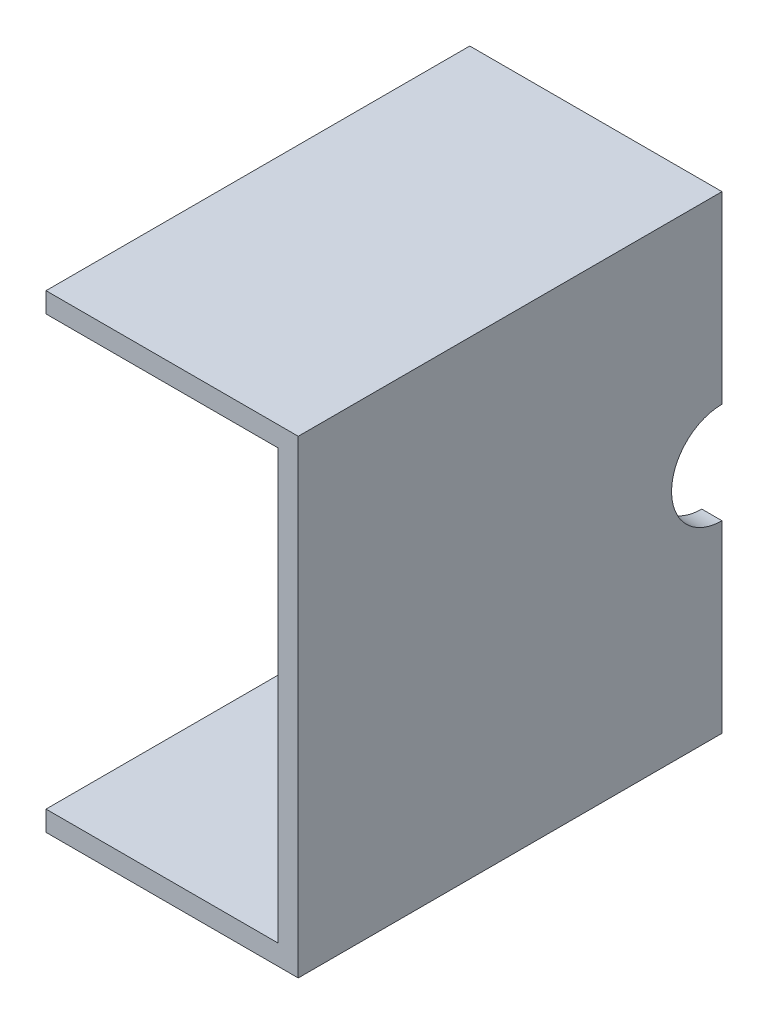
SolidWorks part; units mm, degrees
ref_plane "Front Plane" through (0, 0, 0) normal (0, 0, 1) x (1, 0, 0)
ref_plane "Top Plane" through (0, 0, 0) normal (0, 1, 0) x (1, 0, 0)
ref_plane "Right Plane" through (0, 0, 0) normal (1, 0, 0) x (0, 0, -1)
sketch "Sketch1" plane through (0, 0, 0) normal (1, 0, 0) x (0, 0, -1)
  line L1 (-21, -23.25) -> (21, -23.25)
  line L2 (-21, -23.25) -> (-21, 23.25)
  line L3 (-21, 23.25) -> (21, 23.25)
  line L4 (21, -23.25) -> (21, 23.25)
  line L5 (-21, -23.25) -> (21, 23.25) construction
  line L6 (-21, 23.25) -> (21, -23.25) construction
  point P0 (0, 0)
  dimension "D1" = 42
  dimension "D2" = 46.5
extrude "Boss-Extrude1" add sketch "Sketch1" along normal blind 2
sketch "Sketch2" plane through (0, 0, 0) normal (-1, 0, 0) x (0, 0, 1)
  line L0 (21, 23.25) -> (21, -23.25) construction
  line L1 (-21, -23.25) -> (21, -23.25)
  line L2 (-21, -23.25) -> (-21, -21.25)
  line L3 (-21, -21.25) -> (21, -21.25)
  line L4 (21, -23.25) -> (21, -21.25)
  dimension "D1" = 2
extrude "Boss-Extrude2" add sketch "Sketch2" along normal blind 23
sketch "Sketch3" plane through (2, 0, 0) normal (1, 0, 0) x (0, 0, -1)
  line L0 (21, -23.25) -> (21, 23.25) construction
  line L1 (21, -5) -> (21, 5)
  arc A0 (21, -5) -> (21, 5) centre (21, 0) cw
  dimension "D1" = 5
extrude "Cut-Extrude1" cut sketch "Sketch3" against normal blind 23
sketch "Sketch4" plane through (0, 0, 0) normal (-1, 0, 0) x (0, 0, 1)
  line L0 (-21, 23.25) -> (21, 23.25) construction
  line L1 (21, 23.25) -> (-21, 23.25)
  line L2 (21, 23.25) -> (21, 21.25)
  line L4 (-21, 23.25) -> (-21, 21.25)
  line L5 (21, 23.25) -> (21, -21.25) construction
  line L6 (-21, 5) -> (-21, 23.25) construction
  line L7 (3.2, 21.25) -> (4.5, 19.95)
  line L8 (4.5, 19.95) -> (-4.5, 19.95)
  line L11 (-3.2, 21.25) -> (-21, 21.25)
  line L12 (3.2, 21.25) -> (21, 21.25)
  line L13 (-4.5, 19.95) -> (-3.2, 21.25)
  point P12 (-5.7239, 19.95)
  point P15 (0, 19.95)
  point P24 (0, 23.25)
  dimension "D1" = 2
  dimension "D2" = 1.3
  dimension "D3" = 9
extrude "Boss-Extrude3" add sketch "Sketch4" along normal blind 23
sketch "Sketch5" [suppressed] plane through (0, 23.25, 0) normal (0, 1, 0) x (1, 0, 0)
  line L0 (2, 21) -> (-23, 21) construction
  line L1 (2, 21) -> (2, -21) construction
  line L2 (2, 16) -> (2, 21)
  line L3 (2, 21) -> (-3, 21)
  arc A0 (-3, 21) -> (2, 16) centre (2, 21) ccw
  dimension "D1" = 5
